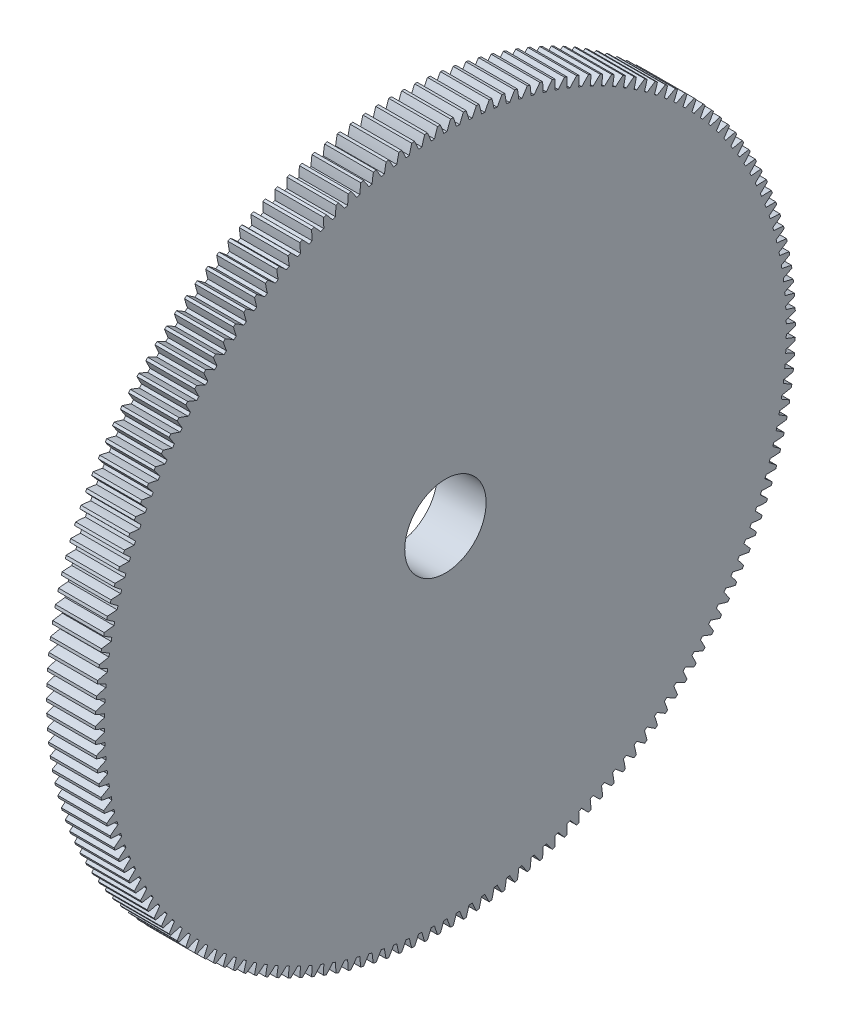
SolidWorks part; units mm, degrees
ref_plane "Plane1" through (0, 0, 0) normal (0, 0, 1) x (1, 0, 0)
ref_plane "Plane2" through (0, 0, 0) normal (0, 1, 0) x (1, 0, 0)
ref_plane "Plane3" through (0, 0, 0) normal (1, 0, 0) x (0, 0, -1)
other "Configuration Table"
sketch "HoldingSke" plane through (0, 0, 0) normal (0, 1, 0) x (1, 0, 0)
  line L0 (0, 0) -> (-0.9848, -0.1736)
  line L1 (-15, 0) -> (100, 0) construction
  line L2 (0, 0) -> (-2.1039, 2.3779)
  line L3 (0, 0) -> (-11.863, 4.5341)
  line L4 (0, 0) -> (-8.5048, 1.4996)
  line L5 (0, 0) -> (-46.8476, -17.4728)
  line L6 (0, 0) -> (-9.9476, -6.7116)
  line L7 (-2.1039, 2.3779) -> (8.6586, 51.2059)
  line L8 (-76.2, 54.61) -> (-73.4, 54.61)
  line L9 (-71.009, 38.7566) -> (-53.1078, 45.2721)
  line L10 (-76.2, 71.12) -> (104.1128, 71.12)
  line L11 (0, 0) -> (-12, 0)
  line L12 (-76.2, 101.6) -> (-76.162, 101.6)
  line L13 (24.9733, 27.94) -> (52.9518, 28.4284)
  line L14 (24.9733, 27.94) -> (24.9743, 27.94)
  line L15 (24.9733, 27.94) -> (100.4006, 29.5858)
  line L16 (-63.627, -1) -> (-12.827, -1)
  circle A0 centre (0, 0) radius 10
  circle A1 centre (0, 0) radius 37.5
  circle A2 centre (0, 0) radius 37.5
  circle A3 centre (0, 0) radius 10
  dimension "MHD" = 75
  dimension "Hub_dia" = 75
  dimension "Bore" = 20
  dimension "MBD" = 20
  dimension "Num_teeth" = 170
  dimension "Pitch" = 1
  dimension "Overall_len" = 50
  dimension "Show_teeth" = 170
  dimension "Thickness" = 12
  dimension "OAL" = 50.0001
  dimension "T_dim" = 2.8
  dimension "Ap" = 20
  dimension "H" = 19.05
  dimension "Pitch_radius" = 180.3128
  dimension "Width" = 12
  dimension "Backlash" = 0.038
  dimension "Addendum_fac" = 1
  dimension "Dedendum_fac" = 1.25
  dimension "Clearance_fac" = 0.25
  dimension "Dedendum_add" = 0.001
  dimension "Module" = 1
sketch "BasProSke" plane through (0, 0, 0) normal (0, 1, 0) x (1, 0, 0)
  line L0 (-10, 0) -> (60, 0) construction
  line L1 (0, 0) -> (0, 86)
  line L2 (0, 0) -> (12, 0)
  line L3 (12, 0) -> (12, 86)
  line L4 (12, 86) -> (0, 86)
  dimension "Thickness" = 12
  dimension "Diameter" = 172
revolve "Base-Revolve" add sketch "BasProSke" angle 360 about L0
sketch "TooCutSke" plane through (0, 0, 0) normal (1, 0, 0) x (0, 0, -1)
  line L1 (0, 0) -> (0, 107) construction
  line L2 (0, 0) -> (-0.8519, 84.9957) construction
  line L3 (0, 0) -> (-3.1413, 169.9649) construction
  line L4 (-0.8519, 84.9957) -> (-1.5707, 84.9824) construction
  arc A0 (0.4048, 83.748) -> (-0.4048, 83.748) centre (0, 0) ccw
  arc A1 (1.2591, 86.0162) -> (-1.2591, 86.0162) centre (0, 0) ccw
  circle A2 centre (0, 0) radius 85 construction
  circle A3 centre (0, 0) radius 79.8739 construction
  arc A4 (-0.4048, 83.748) -> (-1.2591, 86.0162) centre (-32.6295, 72.9051) ccw
  arc A5 (1.2591, 86.0162) -> (0.4048, 83.748) centre (32.6295, 72.9051) ccw
  dimension "Root_dia" = 167.498
  dimension "Overcut_dia" = 172.0508
  dimension "Pitch_dia" = 170
  dimension "Base_dia" = 159.7477
  dimension "Flank_rad" = 34
  dimension "Half_ang" = 1.059
  dimension "Half_CT" = 0.7189
extrude "ToothCut" cut sketch "TooCutSke" along normal through all
fillet "Breaks" [suppressed] radius 0.02
fillet "RootFillets" [suppressed] radius 0.251
pattern_circular "TeethCuts" count 170 every 2.118 about axis through (-10, 0, 0) along (1, 0, 0) of "ToothCut", "RootFillets", "Breaks"
sketch "HubNeaOneSke" plane through (0, 0, 0) normal (-1, 0, 0) x (0, 0, 1)
  circle A0 centre (0, 0) radius 37.5
  dimension "Diameter" = 75
extrude "HubNearOne" [suppressed] add sketch "HubNeaOneSke" along normal blind 38.0001
sketch "HubNeaBotSke" plane through (0, 0, 0) normal (-1, 0, 0) x (0, 0, 1)
  circle A0 centre (0, 0) radius 37.5
  dimension "Diameter" = 75
extrude "HubNearBoth" [suppressed] add sketch "HubNeaBotSke" along normal blind 19
ref_plane "FarPln" through (12, 0, 0) normal (1, 0, 0) x (0, 0, -1)
sketch "HubFarSke" plane through (12, 0, 0) normal (1, 0, 0) x (0, 0, -1)
  circle A0 centre (0, 0) radius 37.5
  dimension "Diameter" = 75
extrude "HubFar" [suppressed] add sketch "HubFarSke" along normal blind 19
sketch "BorSke" plane through (0, 0, 0) normal (1, 0, 0) x (0, 0, -1)
  circle A0 centre (0, 0) radius 10
  dimension "Diameter" = 20
extrude "Bore" cut sketch "BorSke" along normal mid plane 100.0001
sketch "KeySke" plane through (0, 0, 0) normal (1, 0, 0) x (0, 0, -1)
  line L0 (-3, 0) -> (-3, 12.8)
  line L1 (-3, 12.8) -> (3, 12.8)
  line L2 (3, 12.8) -> (3, 0)
  line L3 (0, 0) -> (0, 34) construction
  line L4 (-3, 0) -> (3, 0)
  dimension "Offset" = 12.8
  dimension "Width" = 6
extrude "Keyway" [suppressed] cut sketch "KeySke" along normal mid plane 100.0001
pattern_circular "Keyway2" [suppressed] count 2 every 90 about axis through (-10, 0, 0) along (1, 0, 0)
equation "' \"Module@HoldingSke\" = 6.35"
equation "' \"Num_teeth@HoldingSke\" = 12"
equation "' \"Ap@HoldingSke\" =  20"
equation "' \"Ap@HoldingSke\" = 20"
equation "' \"Width@HoldingSke\" = 0.5 * 25.4"
equation "' \"Hub_dia@HoldingSke\"= 1 * 25.4"
equation "' \"Hub_dia@HoldingSke\" = 1 * 25.4"
equation "' \"Overall_len@HoldingSke\" = 1.0 * 25.4"
equation "' \"Bore@HoldingSke\" = 0.75 * 25.4"
equation "' \"T_dim@HoldingSke\" = 0.1 * 25.4"
equation "' \"Width@KeySke\" = 0.25 * 25.4"
equation "' \"Show_teeth@HoldingSke\" = 13"
equation "' \"Backlash@HoldingSke\" = 0.009 * 25.4"
equation "' \"Addendum_fac@HoldingSke\" = 1.0"
equation "' \"Dedendum_fac@HoldingSke\" = 1.25"
equation "' \"Dedendum_add@HoldingSke\" = 0.00005 * 25.4"
equation "' \"Clearance_fac@HoldingSke\" = 0.25"
equation "\"Pitch@HoldingSke\" = 1 / \"Module@HoldingSke\""
equation "\"Overcut_dia@TooCutSke\" = (\"Num_teeth@HoldingSke\" + 2 * \"Addendum_fac@HoldingSke\") / \"Pitch@HoldingSke\" + 0.002 * 25.4"
equation "\"Pitch_dia@TooCutSke\" = \"Num_teeth@HoldingSke\" / \"Pitch@HoldingSke\""
equation "\"Base_dia@TooCutSke\" = \"Num_teeth@HoldingSke\" / \"Pitch@HoldingSke\" * cos((\"Ap@HoldingSke\"  * 3.14159265 / 180))"
equation "\"Root_dia@TooCutSke\" = (\"Num_teeth@HoldingSke\" + 2) / \"Pitch@HoldingSke\" - 2 * (\"Addendum_fac@HoldingSke\" + \"Dedendum_fac@HoldingSke\") / \"Pitch@HoldingSke\" - \"Dedendum_add@HoldingSke\" * 2"
equation "\"Half_ang@TooCutSke\" = 180 / \"Num_teeth@HoldingSke\""
equation "\"Half_CT@TooCutSke\" = \"Num_teeth@HoldingSke\" / \"Pitch@HoldingSke\" * sin((3.14159265 / 2 / \"Num_teeth@HoldingSke\")) / 2 - 7 * \"Backlash@HoldingSke\" / 4"
equation "\"Flank_rad@TooCutSke\" = \"Num_teeth@HoldingSke\" / \"Pitch@HoldingSke\" / 5"
equation "\"Radius@RootFillets\" = \"Clearance_fac@HoldingSke\" / \"Pitch@HoldingSke\" + \"Dedendum_add@HoldingSke\""
equation "\"Break_rad@Breaks\" = 0.02 / \"Pitch@HoldingSke\""
equation "\"Thickness@HoldingSke\" = \"Width@HoldingSke\""
equation "\"OAL@HoldingSke\" = \"Thickness@HoldingSke\""
equation "\"MHD@HoldingSke\" = (\"Num_teeth@HoldingSke\" + 2) / \"Pitch@HoldingSke\" - 2 * (\"Addendum_fac@HoldingSke\" + \"Dedendum_fac@HoldingSke\")  / \"Pitch@HoldingSke\" - \"Dedendum_add@HoldingSke\" * 2"
equation "\"MBD@HoldingSke\" = (\"Num_teeth@HoldingSke\" + 2) / \"Pitch@HoldingSke\" - 2 * (\"Addendum_fac@HoldingSke\" + \"Dedendum_fac@HoldingSke\")  / \"Pitch@HoldingSke\" - \"Dedendum_add@HoldingSke\" * 2 - 0.002 * 25.4"
equation "\"MHD@HoldingSke\" = ((sgn( \"MHD@HoldingSke\" - \"Hub_dia@HoldingSke\" )-1)*( \"MHD@HoldingSke\" - \"Hub_dia@HoldingSke\" ))/-2+ \"Hub_dia@HoldingSke\""
equation "\"MBD@HoldingSke\" = ((sgn( \"MBD@HoldingSke\" - \"Bore@HoldingSke\" )-1)*( \"MBD@HoldingSke\" - \"Bore@HoldingSke\" ))/-2+ \"Bore@HoldingSke\""
equation "\"OAL@HoldingSke\" = ((sgn( \"OAL@HoldingSke\" - \"Overall_len@HoldingSke\" )+1)*( \"OAL@HoldingSke\" - \"Overall_len@HoldingSke\" ))/2 + \"Overall_len@HoldingSke\" + 0.000002 * 25.4"
equation "\"Num_teeth@TeethCuts\" = int( \"Show_teeth@HoldingSke\" ) + 1"
equation "\"Num_teeth@TeethCuts\" = ((sgn( \"Num_teeth@TeethCuts\" - \"Num_teeth@HoldingSke\" )-1)*( \"Num_teeth@TeethCuts\" - \"Num_teeth@HoldingSke\" ))/-2+ \"Num_teeth@HoldingSke\""
equation "\"Num_teeth@TeethCuts\" = ((sgn( \"Num_teeth@TeethCuts\" - 2.0)+1)*( \"Num_teeth@TeethCuts\" - 2.0))/2 +2.0"
equation "\"Angle@TeethCuts\" = 360.0 / \"Num_teeth@HoldingSke\""
equation "\"Diameter@BasProSke\" = (\"Num_teeth@HoldingSke\" + 2 * \"Addendum_fac@HoldingSke\") / \"Pitch@HoldingSke\""
equation "\"Thickness@BasProSke\"  = \"Thickness@HoldingSke\""
equation "' \"Fillet_rad@BasProSke\" =  \"Thickness@HoldingSke\" * 0.05"
equation "' \"Fillet_rad@BasProSke\" = \"Thickness@HoldingSke\" * 0.05"
equation "\"MHD@HoldingSke\" = ((sgn( \"MHD@HoldingSke\" - \"Root_dia@TooCutSke\" )-1)*( \"MHD@HoldingSke\" - \"Root_dia@TooCutSke\" ))/-2+ \"Root_dia@TooCutSke\""
equation "\"Diameter@HubNeaOneSke\" = \"MHD@HoldingSke\""
equation "\"Length@HubNearOne\" = \"OAL@HoldingSke\" - \"Thickness@BasProSke\""
equation "\"Diameter@HubNeaBotSke\" = \"MHD@HoldingSke\""
equation "\"Length@HubNearBoth\" = ( \"OAL@HoldingSke\" - \"Thickness@BasProSke\" ) / 2.0"
equation "\"Thickness@FarPln\" = \"Thickness@BasProSke\""
equation "\"Diameter@HubFarSke\" = \"MHD@HoldingSke\""
equation "\"Length@HubFar\" = ( \"OAL@HoldingSke\" - \"Thickness@BasProSke\" ) / 2.0"
equation "\"Diameter@BorSke\" = \"MBD@HoldingSke\""
equation "\"D1@Bore\" = \"OAL@HoldingSke\" * 2.0"
equation "\"D1@Keyway\" = \"OAL@HoldingSke\" * 2.0"
equation "\"Offset@KeySke\" = \"T_dim@HoldingSke\" + \"MBD@HoldingSke\" / 2.0"
